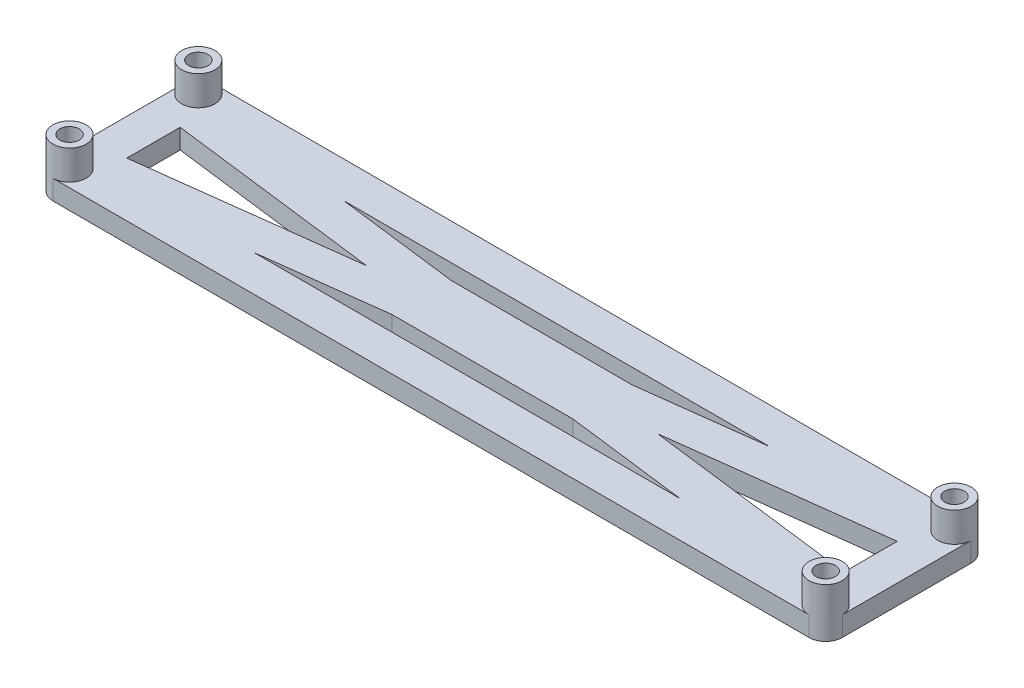
SolidWorks part; units mm, degrees
ref_plane "Front Plane" through (0, 0, 0) normal (0, 0, 1) x (1, 0, 0)
ref_plane "Top Plane" through (0, 0, 0) normal (0, 1, 0) x (1, 0, 0)
ref_plane "Right Plane" through (0, 0, 0) normal (1, 0, 0) x (0, 0, -1)
sketch "Sketch2" plane through (0, 0, 0) normal (0, 1, 0) x (1, 0, 0)
  line L1 (-40.05, 8.225) -> (40.05, 8.225)
  line L6 (-40.05, 8.225) -> (-40.05, -8.225)
  line L7 (-40.05, -8.225) -> (40.05, -8.225)
  line L8 (40.05, 8.225) -> (40.05, -8.225)
  line L9 (-40.05, 8.225) -> (40.05, -8.225) construction
  line L10 (-40.05, -8.225) -> (40.05, 8.225) construction
  point P0 (0, 0)
  dimension "D1" = 80.1
  dimension "D2" = 16.45
extrude "Extrude-Thin1" add sketch "Sketch2" along normal blind 2 thin
sketch "Sketch3" plane through (0, 2, 0) normal (0, 1, 0) x (1, 0, 0)
  line L0 (-36.38, 4.555) -> (36.38, -4.555)
  line L1 (36.38, 4.555) -> (-36.38, -4.555)
  line L2 (36.38, -4.555) -> (36.38, 4.555) construction
  line L4 (36.38, 4.555) -> (-36.38, 4.555) construction
  point P2 (-38.36, 6.39)
  point P3 (-36.38, 4.555)
  point P6 (-36.38, -4.555)
  point P7 (36.38, 4.555)
  point P10 (36.38, 4.555)
  point P12 (36.38, -4.555)
  point P14 (36.38, -4.555)
extrude "Extrude-Thin2" add sketch "Sketch3" against normal through all thin thin type mid plane wall 3.67
sketch "Sketch6" plane through (0, 2, 0) normal (0, 1, 0) x (1, 0, 0)
  line L0 (0, -1.8493) -> (-21.6097, -4.555) construction
  line L1 (-9.1902, 3) -> (9.1902, 3)
  line L2 (-9.1902, 3) -> (-9.1902, -3)
  line L3 (-9.1902, -3) -> (9.1902, -3)
  line L4 (9.1902, 3) -> (9.1902, -3)
  line L5 (-9.1902, 3) -> (9.1902, -3) construction
  line L6 (-9.1902, -3) -> (9.1902, 3) construction
  point P0 (0, 0)
  point P6 (-9.0231, -2.9791)
  dimension "D2" = 6
extrude "Boss-Extrude2" add sketch "Sketch6" against normal through all
sketch "Sketch4" plane through (0, 2, 0) normal (0, 1, 0) x (1, 0, 0)
  line L0 (0, 19.5222) -> (0, -18.4444) construction
  line L1 (-38.36, 6.535) -> (-38.36, 8.225) construction
  line L2 (40.05, 8.225) -> (-40.05, 8.225) construction
  line L3 (-38.36, 6.535) -> (-40.05, 6.535) construction
  line L4 (-40.05, 8.225) -> (-40.05, -8.225) construction
  circle A8 centre (-38.36, 6.535) radius 0.985
  dimension "D1" = 78.69
  dimension "D2" = 74.75
ref_plane "Plane2" through (5.9, 0, 0) normal (1, 0, 0) x (0, 0, -1)
sketch "Sketch7" plane through (5.9, 0, 0) normal (1, 0, 0) x (0, 0, -1)
  line L0 (-3, -3.1) -> (-3, 0)
  line L2 (-3, 0) -> (3, 0)
  line L3 (3, 0) -> (3, -3.1)
  arc A0 (-3, -3.1) -> (3, -3.1) centre (0, -3.1) ccw
  circle A1 centre (0, -3.1) radius 1.375
  point P1 (0, 0)
  point P3 (3, 0)
  point P7 (3, 0)
  point P8 (0, 0)
  dimension "D2" = 6
  dimension "D3" = 2.75
  dimension "D1" = 0.1
extrude "Boss-Extrude3" add sketch "Sketch7" against normal blind 3.8
pattern_linear "LPattern1" count 2 spacing 8 along (-1, 0, 0) of "Boss-Extrude3"
sketch "Sketch8" plane through (0, 2, 0) normal (0, 1, 0) x (1, 0, 0)
  line L0 (40.05, 8.225) -> (-40.05, 8.225) construction
  line L1 (-40.05, 8.225) -> (-40.05, -8.225) construction
  circle A0 centre (-38.36, 6.535) radius 1.69
  point P6 (0, 0)
fillet "Fillet2" radius 1.69 4 edges at (-40.05, 1, -8.225) (-40.05, 1, 8.225) (40.05, 1, -8.225) (40.05, 1, 8.225)
extrude "Boss-Extrude4" add sketch "Sketch8" along normal blind 3
extrude "Cut-Extrude1" cut sketch "Sketch4" against normal offset from surface (4 mm away) 1 from surface at 3 starting at face at (-38.36, 5, -4.845)
mirror "Mirror1" about plane through (0, 0, 0) normal (0, 0, 1) of "Boss-Extrude4", "Cut-Extrude1"
mirror "Mirror2" about plane through (0, 0, 0) normal (1, 0, 0) of "Mirror1", "Boss-Extrude4", "Cut-Extrude1"
equation "\"JointWidth\"= 4"
equation "\"D1@Boss-Extrude3\"=\"JointWidth\" - 0.2"
equation "\"D3@LPattern1\"=\"JointWidth\"*2"
